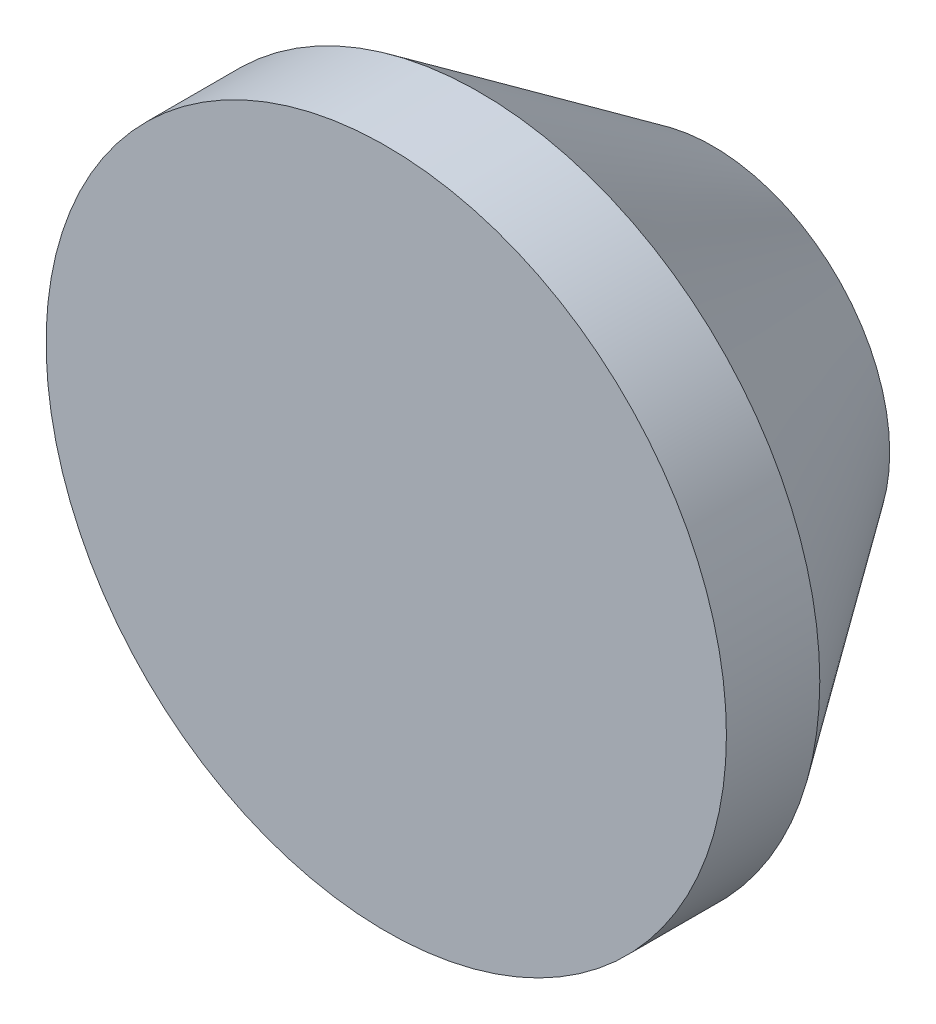
SolidWorks part; units mm, degrees
ref_plane "Front Plane" through (0, 0, 0) normal (0, 0, 1) x (1, 0, 0)
ref_plane "Top Plane" through (0, 0, 0) normal (0, 1, 0) x (1, 0, 0)
ref_plane "Right Plane" through (0, 0, 0) normal (1, 0, 0) x (0, 0, -1)
sketch "Sketch1" plane through (0, 0, 0) normal (0, 0, 1) x (1, 0, 0)
  circle A0 centre (0, 0) radius 3
  circle A1 centre (0, 0) radius 12.5
  dimension "D1" = 6
  dimension "D2" = 25
extrude "Boss-Extrude1" add sketch "Sketch1" along normal blind 12
sketch "Sketch2" plane through (0, 0, 12) normal (0, 0, 1) x (1, 0, 0)
  circle A0 centre (0, 0) radius 3
  dimension "D1" = 6
extrude "Boss-Extrude2" add sketch "Sketch2" against normal blind 1
chamfer "Chamfer1" distance 6 angle 55 1 edges at (12.5, 0, 0)
